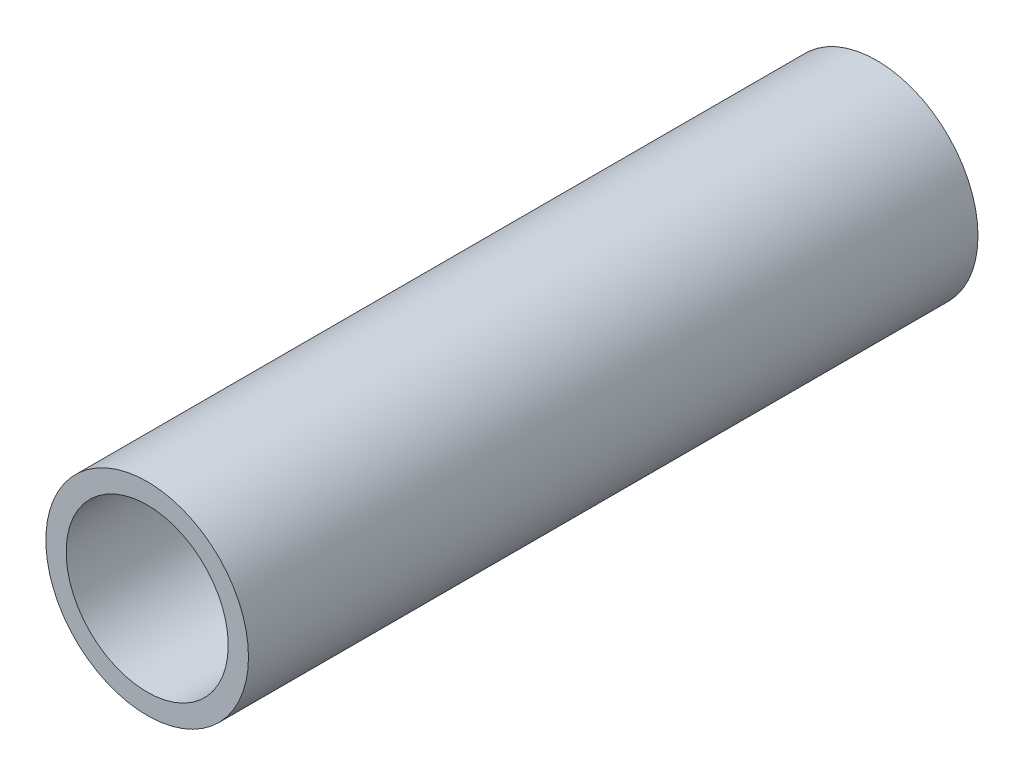
SolidWorks part; units mm, degrees
ref_plane "Front Plane" through (0, 0, 0) normal (0, 0, 1) x (1, 0, 0)
ref_plane "Top Plane" through (0, 0, 0) normal (0, 1, 0) x (1, 0, 0)
ref_plane "Right Plane" through (0, 0, 0) normal (1, 0, 0) x (0, 0, -1)
sketch "Sketch1" plane through (0, 0, 0) normal (0, 0, 1) x (1, 0, 0)
  circle A0 centre (0, 0) radius 1.25
  circle A1 centre (0, 0) radius 1
  dimension "D1" = 2
  dimension "D2" = 2.5
extrude "Boss-Extrude1" add sketch "Sketch1" along normal blind 9
